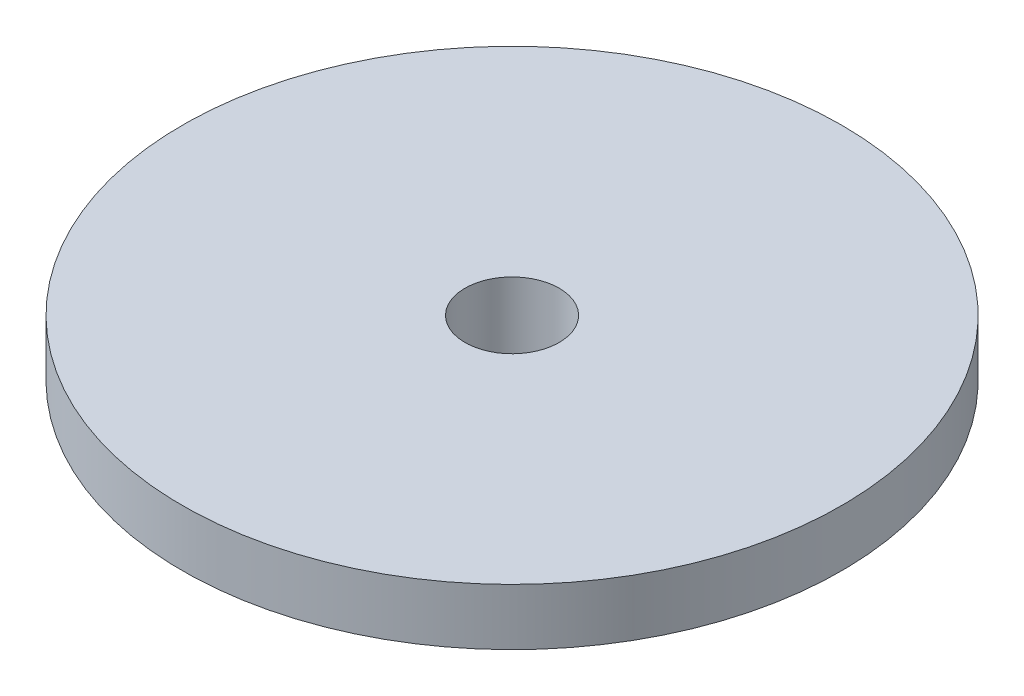
SolidWorks part; units mm, degrees
ref_plane "Front Plane" through (0, 0, 0) normal (0, 0, 1) x (1, 0, 0)
ref_plane "Top Plane" through (0, 0, 0) normal (0, 1, 0) x (1, 0, 0)
ref_plane "Right Plane" through (0, 0, 0) normal (1, 0, 0) x (0, 0, -1)
sketch "Sketch1" plane through (0, 0, 0) normal (0, 0, 1) x (1, 0, 0)
  line L0 (0, 0) -> (0, 10)
  line L1 (0, 10) -> (17.5, 10)
  line L2 (17.5, 10) -> (17.5, 7)
  line L4 (7, 0) -> (0, 0)
  line L5 (17.5, 7) -> (7, 0)
  dimension "D1" = 17.5
  dimension "D2" = 7
  dimension "D3" = 3
  dimension "D4" = 10
revolve "Revolve1" add sketch "Sketch1" angle 360 about L0
sketch "Sketch4" plane through (0, 0, 0) normal (0, -1, 0) x (-1, 0, 0)
  point P0 (0, 0)
sketch "Sketch10" plane through (0, 0, 0) normal (0, -1, 0) x (1, 0, 0)
  circle A0 centre (0, 0) radius 2.5
  dimension "D1" = 5
extrude "Cut-Extrude1" cut sketch "Sketch10" against normal through all
